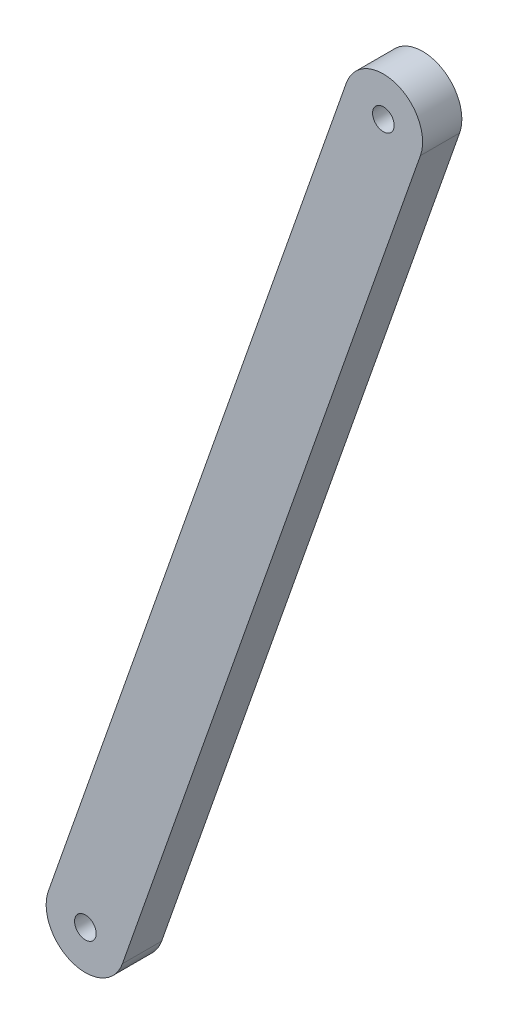
SolidWorks part; units mm, degrees
ref_plane "Front Plane" through (0, 0, 0) normal (0, 0, 1) x (1, 0, 0)
ref_plane "Top Plane" through (0, 0, 0) normal (0, 1, 0) x (1, 0, 0)
ref_plane "Right Plane" through (0, 0, 0) normal (1, 0, 0) x (0, 0, -1)
sketch "Sketch1" plane through (0, 0, 0) normal (0, 0, 1) x (1, 0, 0)
  line L0 (0, 0) -> (40.3547, 419.1) construction
  line L1 (40.3547, 419.1) -> (159.2585, 419.1) construction
  line L2 (159.2585, 419.1) -> (159.2585, 0) construction
  line L3 (159.2585, 0) -> (0, 0) construction
  line L4 (159.2585, -1000) -> (159.2585, 49000) construction
  line L5 (2.0164, 20.9415) -> (40.3547, 419.1) construction
  line L6 (2.0164, 20.9415) -> (41.8323, 17.1077) construction
  line L7 (40.3547, 419.1) -> (80.1706, 415.2662) construction
  line L8 (41.8323, 17.1077) -> (80.1706, 415.2662) construction
  line L9 (64.0085, -1000) -> (64.0085, 49000) construction
  line L10 (-42.7214, 317.5) -> (-118.5706, 324.8034) construction
  line L11 (-20.0013, 414.3375) -> (40.196, 414.3375) construction
  line L12 (-1162.1335, 304.8) -> (48837.8665, 304.8) construction
  line L13 (-120.1415, 292.1) -> (-43.9415, 292.1) construction
  line L14 (-118.5706, 324.8034) -> (-43.9415, 292.1) construction
  line L15 (-42.7214, 317.5) -> (-120.1415, 292.1) construction
  line L16 (40.196, 338.1375) -> (-20.0013, 338.1375) construction
  line L17 (-128.0517, 325.7164) -> (29.8985, 310.5075)
  line L18 (-128.0517, 325.7164) -> (-127.4431, 332.0371)
  line L19 (-127.4431, 332.0371) -> (40.3547, 419.1)
  line L20 (40.3547, 419.1) -> (100.3991, 419.1)
  line L21 (108.4585, 419.1) -> (108.4585, 0) construction
  line L22 (29.8985, 310.5075) -> (0.4102, 4.2603)
  line L23 (0.4102, 4.2603) -> (44.6556, 0)
  line L24 (44.6556, 0) -> (108.4585, 0)
  line L25 (111.8902, 411.8076) -> (159.2585, 311.15)
  line L26 (159.2585, 311.15) -> (159.2585, 304.8)
  line L27 (159.2585, 304.8) -> (108.4585, 280.8941)
  line L28 (108.4585, 280.8941) -> (108.4585, 0)
  line L29 (100.3991, 406.4) -> (28627.168, -40334.0482) construction
  line L30 (107.4945, 405.1489) -> (48105.9225, -8058.269) construction
  line L31 (46.2285, 266.7) -> (77.1396, 255.4859) construction
  line L32 (46.2285, 266.7) -> (77.1396, 277.9141) construction
  line L33 (114.9679, 385.5935) -> (125.3711, 392.878) construction
  line L34 (125.4132, 401.9893) -> (127.6185, 414.4964) construction
  line L35 (77.1396, 277.9141) -> (127.6185, 414.4964) construction
  line L36 (125.3711, 392.878) -> (77.1396, 255.4859) construction
  line L37 (77.1396, 277.9141) -> (64.0085, 277.9141) construction
  line L38 (77.1396, 255.4859) -> (64.0085, 255.4859) construction
  arc A0 (-118.5706, 324.8034) -> (-20.0013, 414.3375) centre (-20.0013, 315.3123) cw construction
  arc A1 (73.5335, 304.8) -> (40.196, 338.1375) centre (40.196, 304.8) ccw construction
  arc A2 (149.7335, 304.8) -> (40.196, 414.3375) centre (40.196, 304.8) ccw construction
  arc A3 (-42.7214, 317.5) -> (-20.0013, 338.1375) centre (-20.0013, 315.3123) cw construction
  arc A4 (100.3991, 419.1) -> (111.8902, 411.8076) centre (100.3991, 406.4) cw
  point P7 (57.6585, 400.05)
  point P17 (149.7335, 304.8)
  point P18 (73.5335, 304.8)
  dimension "D9" = 9.525
  dimension "D14" = 25.4
  dimension "D22" = 12.7
  dimension "D1" = 419.1
  dimension "D2" = 101.6
  dimension "D3" = 19.05
  dimension "D4" = 19.05
  dimension "D5" = 84.5
  dimension "D6" = 40
  dimension "D7" = 400
  dimension "D8" = 95.25
  dimension "D10" = 9.525
  dimension "D11" = 114.3
  dimension "D12" = 76.2
  dimension "D13" = 9.525
  dimension "D15" = 127
  dimension "D16" = 9.525
  dimension "D17" = 203.2
  dimension "D18" = 6.35
  dimension "D19" = 50.8
  dimension "D20" = 44.45
  dimension "D21" = 6.35
  dimension "D23" = 55
  dimension "D24" = 25.4
  dimension "D25" = 12.7
  dimension "D26" = 25.4
  dimension "D27" = 12.7
  dimension "D28" = 17.78
  dimension "D29" = 38.1
  dimension "D30" = 39.88
  dimension "D31" = 10
sketch "Sketch3" plane through (0, 0, 0) normal (0, 0, 1) x (1, 0, 0)
  line L0 (77.1396, 255.4859) -> (125.3711, 392.878) construction
  line L1 (71.1481, 257.5893) -> (119.3796, 394.9813)
  line L2 (83.1312, 253.3826) -> (131.3627, 390.7746)
  arc A0 (71.1481, 257.5893) -> (83.1312, 253.3826) centre (77.1396, 255.4859) ccw
  arc A1 (131.3627, 390.7746) -> (119.3796, 394.9813) centre (125.3711, 392.878) ccw
  circle A2 centre (77.1396, 255.4859) radius 1.75
  circle A3 centre (125.3711, 392.878) radius 1.75
  point P4 (101.2554, 324.1819)
  dimension "D2" = 3.5
  dimension "D1" = 12.7
extrude "Boss-Extrude1" add sketch "Sketch3" along normal blind 6.35
